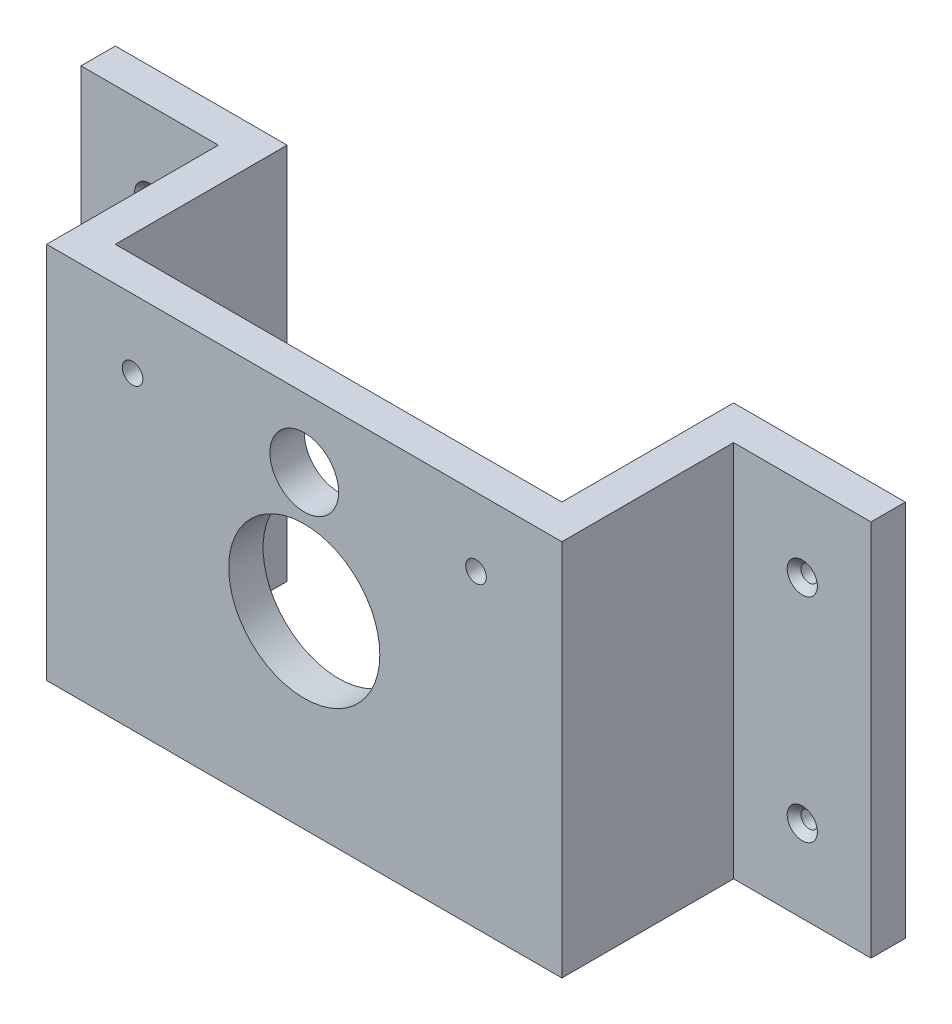
SolidWorks part; units mm, degrees
ref_plane "Ön Düzlem" through (0, 0, 0) normal (0, 0, 1) x (1, 0, 0)
ref_plane "Üst Düzlem" through (0, 0, 0) normal (0, 1, 0) x (1, 0, 0)
ref_plane "Sağ Düzlem" through (0, 0, 0) normal (1, 0, 0) x (0, 0, -1)
sketch "Sketch1" plane through (0, 0, 0) normal (0, 0, 1) x (1, 0, 0)
  line L1 (-37.5, 27.5) -> (37.5, 27.5)
  line L2 (-37.5, 27.5) -> (-37.5, -27.5)
  line L3 (-37.5, -27.5) -> (37.5, -27.5)
  line L4 (37.5, 27.5) -> (37.5, -27.5)
  line L5 (-37.5, 27.5) -> (37.5, -27.5) construction
  line L6 (-37.5, -27.5) -> (37.5, 27.5) construction
  point P0 (0, 0)
  dimension "D1" = 75
  dimension "D2" = 55
extrude "Boss-Extrude1" add sketch "Sketch1" along normal blind 5
sketch "Sketch2" plane through (0, 0, 0) normal (0, 0, -1) x (-1, 0, 0)
  line L0 (37.5, -27.5) -> (-37.5, -27.5) construction
  line L1 (-37.5, 27.5) -> (-32.5, 27.5)
  line L2 (-37.5, 27.5) -> (-37.5, -27.5)
  line L3 (-37.5, -27.5) -> (-32.5, -27.5)
  line L4 (-32.5, 27.5) -> (-32.5, -27.5)
  line L6 (37.5, 27.5) -> (32.5, 27.5)
  line L7 (37.5, 27.5) -> (37.5, -27.5)
  line L8 (37.5, -27.5) -> (32.5, -27.5)
  line L9 (32.5, 27.5) -> (32.5, -27.5)
  dimension "D1" = 5
  dimension "D2" = 5
extrude "Boss-Extrude2" add sketch "Sketch2" along normal blind 25
sketch "Sketch3" plane through (0, 0, 5) normal (0, 0, 1) x (1, 0, 0)
  line L0 (-37.5, 27.5) -> (-37.5, -27.5) construction
  line L1 (37.5, 27.5) -> (-37.5, 27.5) construction
  circle A0 centre (0, 17.5) radius 5
  circle A1 centre (-25, 17.5) radius 1.5
  circle A2 centre (25, 17.5) radius 1.5
  circle A3 centre (0, 0) radius 11
  dimension "D1" = 10
  dimension "D2" = 3
  dimension "D3" = 3
  dimension "D6" = 10
  dimension "D8" = 22
  dimension "D4" = 50
  dimension "D5" = 12.5
  dimension "D7" = 10
extrude "Cut-Extrude1" cut sketch "Sketch3" against normal up to next
sketch "Sketch4" plane through (37.5, 0, 0) normal (1, 0, 0) x (0, 0, -1)
  line L0 (-5, -27.5) -> (25, -27.5) construction
  line L1 (25, 27.5) -> (20, 27.5)
  line L2 (25, 27.5) -> (25, -27.5)
  line L3 (25, -27.5) -> (20, -27.5)
  line L4 (20, 27.5) -> (20, -27.5)
  dimension "D1" = 5
extrude "Boss-Extrude3" add sketch "Sketch4" along normal blind 20
sketch "Sketch5" plane through (-37.5, 0, 0) normal (-1, 0, 0) x (0, 0, 1)
  line L0 (5, -27.5) -> (-25, -27.5) construction
  line L1 (-25, 27.5) -> (-20, 27.5)
  line L2 (-25, 27.5) -> (-25, -27.5)
  line L3 (-25, -27.5) -> (-20, -27.5)
  line L4 (-20, 27.5) -> (-20, -27.5)
  dimension "D1" = 5
extrude "Boss-Extrude4" add sketch "Sketch5" along normal blind 20
hole_wizard "M2 Düz Başlı Makine Vidası İçin Havşa1" positions "Sketch9" profile "Sketch8" countersink size "M2" standard "ANSI Metrik" end condition through all
sketch "Sketch9" plane through (0, 0, -20) normal (0, 0, 1) x (1, 0, 0)
  line L1 (-57.5, -27.5) -> (-57.5, 27.5) construction
  line L2 (-57.5, 27.5) -> (-37.5, 27.5) construction
  line L3 (-57.5, -27.5) -> (-37.5, -27.5) construction
  line L4 (57.5, 27.5) -> (37.5, 27.5) construction
  line L5 (57.5, -27.5) -> (37.5, -27.5) construction
  line L6 (57.5, 27.5) -> (57.5, -27.5) construction
  point P0 (-47.5, 15.5)
  point P2 (-47.5, -15.5)
  point P4 (47.5, 15.5)
  point P6 (47.5, -15.5)
  dimension "D1" = 10
  dimension "D2" = 10
  dimension "D3" = 12
  dimension "D4" = 12
  dimension "D5" = 12
  dimension "D6" = 12
  dimension "D7" = 10
  dimension "D8" = 10
sketch "Sketch8" plane through (-47.5, 15.5, -20) normal (1, 0, 0) x (0, -1, 0)
  line L0 (0, 0) -> (0, 5)
  line L1 (0, 5) -> (1.2, 5)
  line L2 (1.2, 5) -> (1.2, 1)
  line L3 (1.2, 1) -> (2.2, 0)
  line L5 (2.2, 0) -> (0, 0)
  line L6 (-1.2, 1) -> (-2.2, 0) construction
  line L11 (0, -6.35) -> (0, 107.95) construction
  dimension "Thru Hole Dia." = 2.4
  dimension "Thru Hole Depth" = 5
  dimension "Near C'Sink Dia." = 4.4
  dimension "Near C'Sink Angle" = 90
